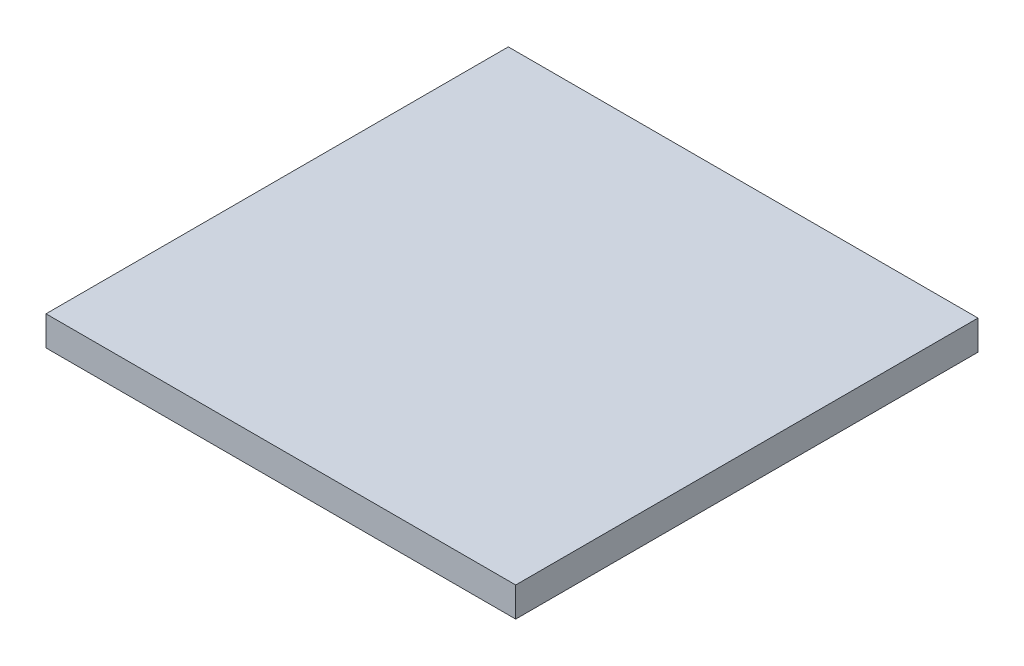
SolidWorks part; units mm, degrees
ref_plane "Alzado" through (0, 0, 0) normal (0, 0, 1) x (1, 0, 0)
ref_plane "Planta" through (0, 0, 0) normal (0, 1, 0) x (1, 0, 0)
ref_plane "Vista lateral" through (0, 0, 0) normal (1, 0, 0) x (0, 0, -1)
sketch "Croquis1" plane through (0, 0, 0) normal (0, 0, 1) x (1, 0, 0)
  line L5 (0, 0) -> (101.6, 0)
  line L6 (0, 0) -> (0, 6.4)
  line L7 (0, 6.4) -> (101.6, 6.4)
  line L8 (101.6, 0) -> (101.6, 6.4)
extrude "Saliente-Extruir1" add sketch "Croquis1" along normal blind 100
